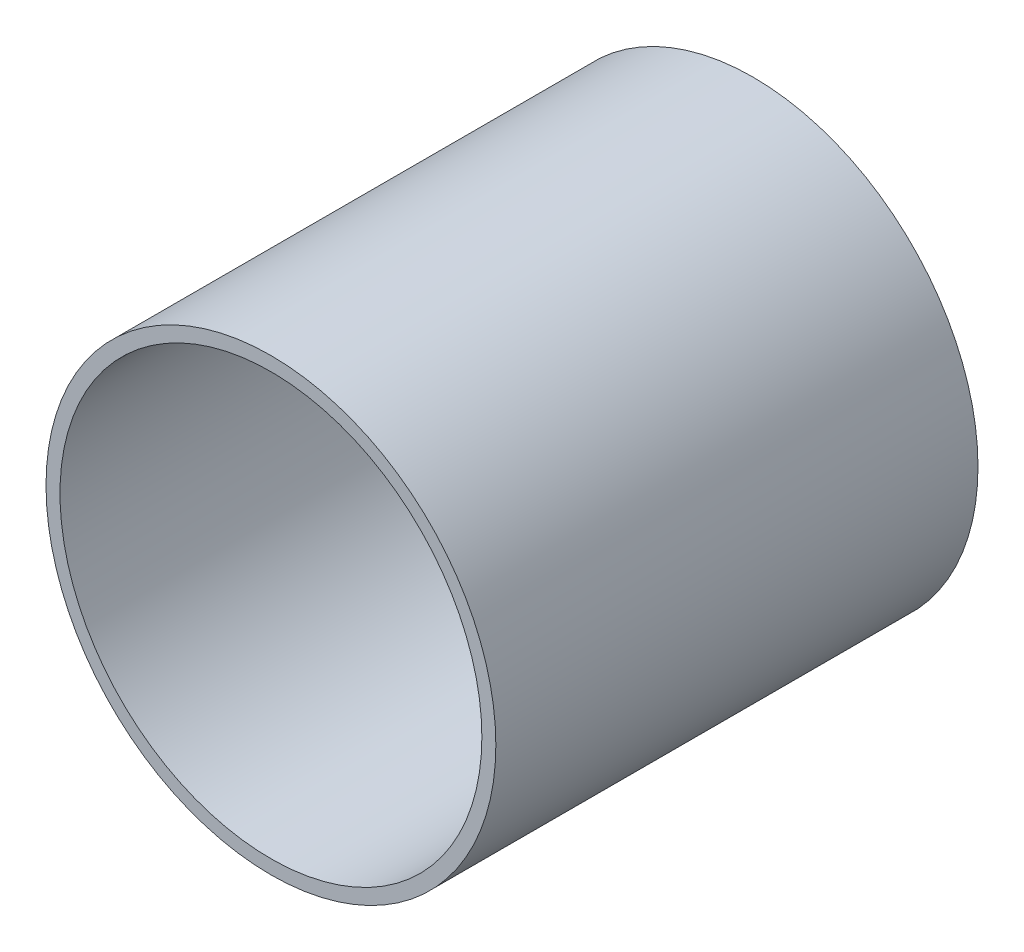
SolidWorks part; units mm, degrees
ref_plane "Front Plane" through (0, 0, 0) normal (0, 0, 1) x (1, 0, 0)
ref_plane "Top Plane" through (0, 0, 0) normal (0, 1, 0) x (1, 0, 0)
ref_plane "Right Plane" through (0, 0, 0) normal (1, 0, 0) x (0, 0, -1)
sketch "Sketch1" plane through (0, 0, 0) normal (0, 0, 1) x (1, 0, 0)
  circle A0 centre (0, 0) radius 22.225
  circle A1 centre (0, 0) radius 23.6982
  dimension "D1" = 44.45
  dimension "D2" = 47.3964
extrude "Boss-Extrude1" add sketch "Sketch1" along normal blind 50.8
